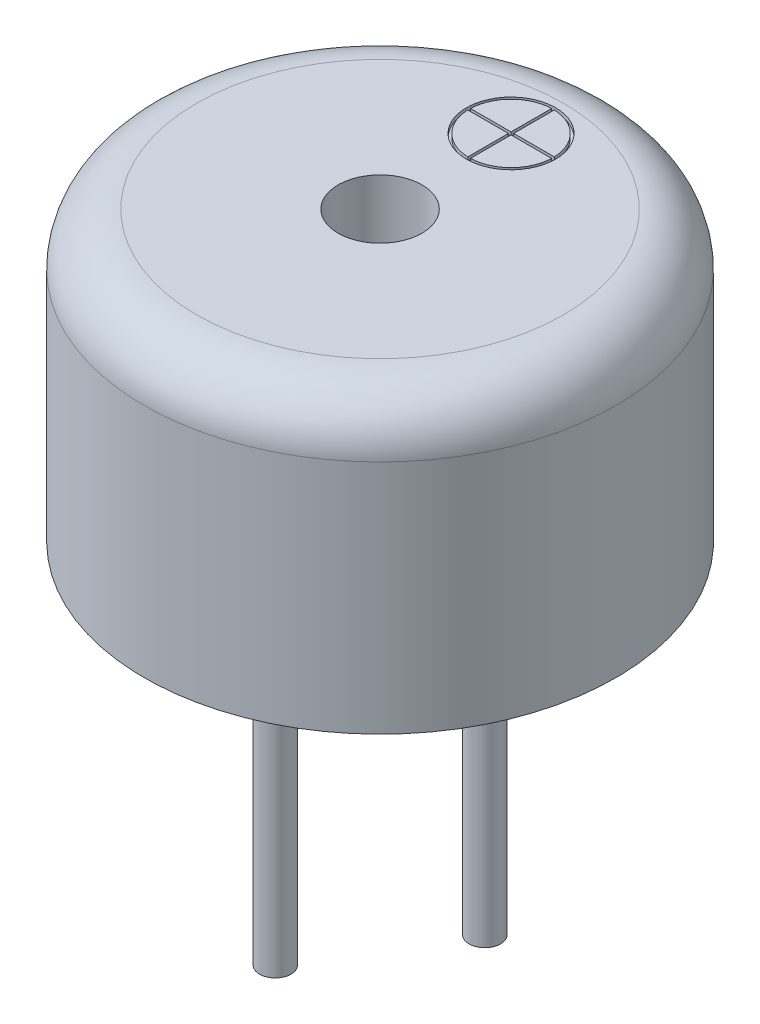
SolidWorks part; units mm, degrees
ref_plane "Front Plane" through (0, 0, 0) normal (0, 0, 1) x (1, 0, 0)
ref_plane "Top Plane" through (0, 0, 0) normal (0, 1, 0) x (1, 0, 0)
ref_plane "Right Plane" through (0, 0, 0) normal (1, 0, 0) x (0, 0, -1)
sketch "Sketch1" plane through (0, 0, 0) normal (0, 0, 1) x (1, 0, 0)
  line L0 (0, 0) -> (0, 11.978) construction
  line L1 (-4.5, 0) -> (-4.5, 4.5)
  line L2 (-3.5, 5.5) -> (0, 5.5)
  line L3 (0, 5.5) -> (0, 0)
  line L4 (0, 0) -> (-4.5, 0)
  arc A0 (-4.5, 4.5) -> (-3.5, 5.5) centre (-3.5, 4.5) cw
  dimension "D1" = 9
  dimension "D3" = 1
  dimension "D2" = 5.5
revolve "Body" add sketch "Sketch1" angle 360 about L0
sketch "Sketch2" plane through (0, 0, 0) normal (0, -1, 0) x (1, 0, 0)
  line L0 (0, 2) -> (0, -2) construction
  circle A0 centre (0, 2) radius 0.3
  circle A1 centre (0, -2) radius 0.3
  point P3 (0, 0)
  dimension "D1" = 0.6
  dimension "D2" = 4
extrude "Leads" add sketch "Sketch2" along normal blind 7.5 separate body
sketch "Sketch3" plane through (0, -7.5, 0) normal (0, -1, 0) x (1, 0, 0)
  circle A0 centre (0, 2) radius 0.3 construction
  circle A1 centre (0, 2) radius 0.3
extrude "Cut-Extrude1" cut sketch "Sketch3" against normal offset from surface (1.5 mm away) 1.5 up to face at (0, -7.5, -2.3)
sketch "Sketch4" plane through (0, 5.5, 0) normal (0, 1, 0) x (1, 0, 0)
  circle A0 centre (0, 0) radius 0.8
  dimension "D1" = 1.6
extrude "Cut-Extrude2" cut sketch "Sketch4" against normal blind 2.5
sketch "Sketch6" plane through (0, 5.5, 0) normal (0, 1, 0) x (1, 0, 0)
  line L0 (0, 3.3255) -> (0, 1.6745)
  line L1 (0.8255, 2.5) -> (-0.8255, 2.5)
  circle A0 centre (0, 2.5) radius 0.8255
  dimension "D1" = 1.651
  dimension "D2" = 2.5
extrude "Cut-Extrude-Thin1" cut sketch "Sketch6" against normal blind 0.0762 thin thin type mid plane wall 0.0508
